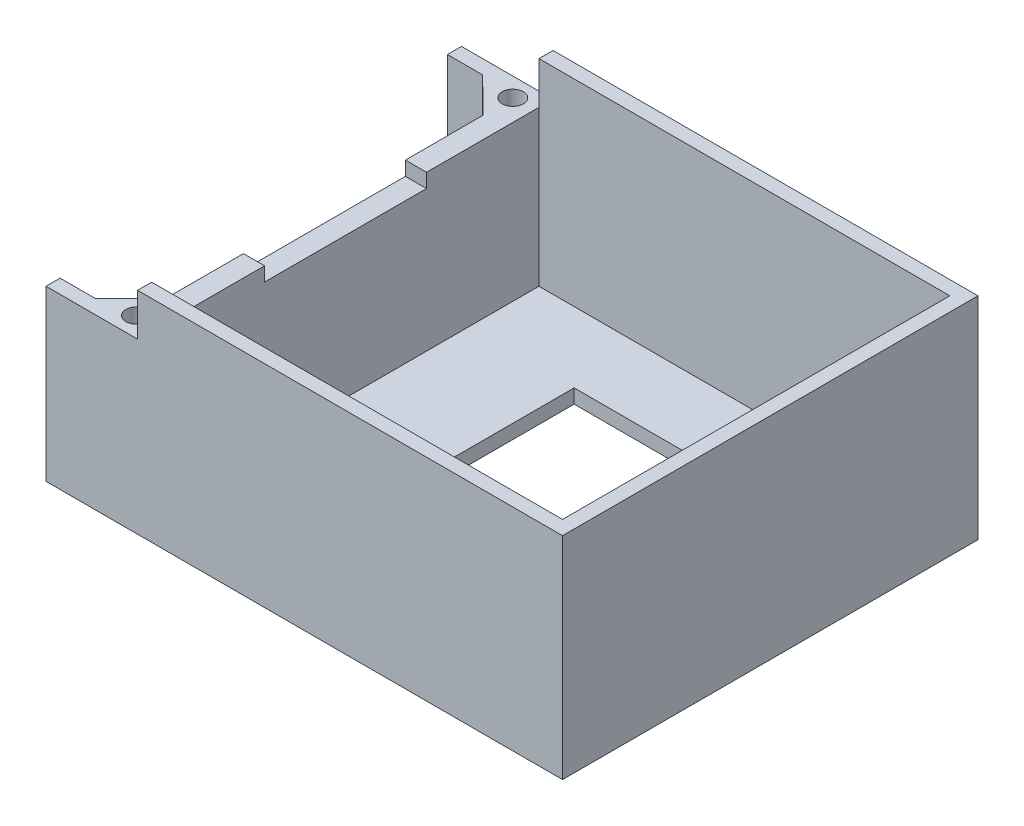
SolidWorks part; units mm, degrees
ref_plane "Front Plane" through (0, 0, 0) normal (0, 0, 1) x (1, 0, 0)
ref_plane "Top Plane" through (0, 0, 0) normal (0, 1, 0) x (1, 0, 0)
ref_plane "Right Plane" through (0, 0, 0) normal (1, 0, 0) x (0, 0, -1)
sketch "Sketch1" plane through (0, 0, 0) normal (0, 1, 0) x (1, 0, 0)
  line L1 (0, 0) -> (70, 0)
  line L2 (0, 0) -> (0, -55)
  line L3 (0, -55) -> (70, -55)
  line L4 (70, 0) -> (70, -55)
  dimension "D1" = 55
  dimension "D2" = 70
extrude "Boss-Extrude1" add sketch "Sketch1" along normal blind 2
sketch "Sketch2" plane through (0, 0, 0) normal (0, 1, 0) x (1, 0, 0)
  line L0 (70, 0) -> (0, 0) construction
  line L1 (-1.3503, 2) -> (72, 2)
  line L2 (-1.3503, 2) -> (-1.3503, -57)
  line L3 (-1.3503, -57) -> (72, -57)
  line L4 (72, 2) -> (72, -57)
  line L5 (0, -55) -> (70, -55) construction
  line L6 (0, 0) -> (0, -55) construction
  line L7 (70, -55) -> (70, 0) construction
  point P5 (-1.3503, 1.4771)
  dimension "D1" = 2
  dimension "D2" = 2
  dimension "D3" = 1.3503
  dimension "D4" = 2
extrude "Boss-Extrude3" add sketch "Sketch2" along normal blind 2
sketch "Sketch3" plane through (0, 2, 0) normal (0, 1, 0) x (1, 0, 0)
  line L0 (-1.3503, 2) -> (72, 2)
  line L1 (72, 2) -> (72, -57)
  line L2 (72, -57) -> (-1.3503, -57)
  line L3 (-1.3503, -57) -> (-1.3503, -55)
  line L4 (-1.3503, 2) -> (-1.3503, -57) construction
  line L5 (-1.3503, -55) -> (70, -55)
  line L6 (70, -55) -> (70, 0)
  line L7 (70, 0) -> (-1.3503, 0)
  line L8 (-1.3503, 0) -> (-1.3503, 2)
  dimension "D1" = 2
  dimension "D2" = 2
extrude "Boss-Extrude4" add sketch "Sketch3" along normal blind 28
sketch "Sketch5" plane through (0, 2, 0) normal (0, 1, 0) x (1, 0, 0)
  line L0 (-1.3503, 0) -> (70, 0) construction
  line L1 (8.6497, 0) -> (11.6497, 0)
  line L2 (8.6497, 0) -> (8.6497, -55)
  line L3 (8.6497, -55) -> (11.6497, -55)
  line L4 (11.6497, 0) -> (11.6497, -55)
  line L5 (70, -55) -> (-1.3503, -55) construction
  line L6 (-1.3503, 0) -> (-1.3503, -55) construction
  line L7 (3.6497, 0) -> (8.6497, -4.9272)
  line L8 (8.6497, -4.9272) -> (8.6497, 0)
  line L9 (3.6497, 0) -> (8.6497, 0)
  line L10 (3.6497, -55) -> (8.6497, -49.9262)
  line L11 (8.6497, -49.9262) -> (8.6497, -55)
  line L12 (3.6497, -55) -> (8.6497, -55)
  line L13 (-1.3503, 0) -> (8.6497, 0) construction
  line L14 (-1.3503, -55) -> (8.6497, -55) construction
  point P17 (3.6497, -55)
  point P18 (8.6497, -4.9272)
  point P20 (0, 0)
  point P21 (0, 0)
  line M8 (-1.3503, -55) -> (70, -55)
  line M10 (70, 0) -> (-1.3503, 0)
  dimension "D1" = 3
  dimension "D2" = 10
  dimension "D3" = 4.9272
extrude "Boss-Extrude5" add sketch "Sketch5" along normal blind 22 contours L4 L2 M10 M8 | L7 L2 M10 | L10 L2 M8
sketch "Sketch14" plane through (0, 30, 0) normal (0, 1, 0) x (1, 0, 0)
  line L1 (-1.3503, 2) -> (11.6497, 2)
  line L2 (-1.3503, 2) -> (-1.3503, 0)
  line L3 (-1.3503, 0) -> (11.6497, 0)
  line L4 (11.6497, 2) -> (11.6497, 0)
  line L5 (-1.3503, -57) -> (11.6497, -57)
  line L6 (-1.3503, -57) -> (-1.3503, -55)
  line L7 (-1.3503, -55) -> (11.6497, -55)
  line L8 (11.6497, -57) -> (11.6497, -55)
extrude "Cut-Extrude5" cut sketch "Sketch14" against normal blind 6
sketch "Sketch15" plane through (0, 24, 0) normal (0, 1, 0) x (1, 0, 0)
  line L0 (3.6497, 0) -> (8.6497, -4.9272) construction
  line L1 (3.6497, -55) -> (8.6497, -49.9262) construction
  circle A2 centre (8.6111, -0.6772) radius 1.5
  circle A3 centre (8.6735, -54.1761) radius 1.5
  dimension "D1" = 3
  dimension "D4" = 3
  dimension "D2" = 3
  dimension "D3" = 4.25
  dimension "D5" = 3
  dimension "D6" = 4.25
extrude "Cut-Extrude6" cut sketch "Sketch15" against normal through all
sketch "Sketch16" plane through (0, 0, 0) normal (0, -1, 0) x (1, 0, 0)
  circle A0 centre (8.6735, 54.1761) radius 2.25
  circle A1 centre (8.6111, 0.6772) radius 2.25
  dimension "D1" = 4.5
  dimension "D2" = 4.5
extrude "Cut-Extrude7" cut sketch "Sketch16" against normal blind 21
sketch "Sketch17" plane through (0, 24, 0) normal (0, 1, 0) x (1, 0, 0)
  line L0 (8.6497, -4.9272) -> (8.6497, -49.9262) construction
  line L1 (8.6497, -38.9634) -> (11.6497, -38.9634)
  line L2 (8.6497, -38.9634) -> (8.6497, -15.9634)
  line L3 (8.6497, -15.9634) -> (11.6497, -15.9634)
  line L4 (11.6497, -38.9634) -> (11.6497, -15.9634)
  line L5 (11.6497, 0) -> (11.6497, -55) construction
  line L7 (11.6497, 0) -> (11.6497, -55) construction
  line L8 (8.6497, -27.4267) -> (11.6497, -27.5) construction
  line L9 (8.6497, -4.9272) -> (8.6497, -49.9262) construction
  line L10 (8.6497, -38.9634) -> (11.6497, -15.9634) construction
  point P8 (11.6497, -27.4634)
  point P17 (10.1497, -27.4634)
  point P18 (10.1497, -27.4634)
  dimension "D1" = 23
extrude "Cut-Extrude8" cut sketch "Sketch17" against normal blind 2
sketch "Sketch18" plane through (0, 2, 0) normal (0, 1, 0) x (1, 0, 0)
  line L0 (40.8249, 0) -> (40.8249, -55) construction
  line L1 (26.6497, -10) -> (63.6497, -10)
  line L2 (26.6497, -10) -> (26.6497, -45)
  line L3 (26.6497, -45) -> (63.6497, -45)
  line L4 (63.6497, -10) -> (63.6497, -45)
  line L5 (40.8249, -10) -> (40.8249, -45) construction
  line L6 (11.6497, 0) -> (70, 0) construction
  line L7 (70, -55) -> (11.6497, -55) construction
  line L8 (11.6497, 0) -> (11.6497, -55) construction
  point P10 (40.8249, -27.5)
  point P13 (40.8249, -27.5)
  dimension "D1" = 15
  dimension "D2" = 35
  dimension "D3" = 37
extrude "Cut-Extrude9" cut sketch "Sketch18" against normal through all
sketch "Sketch19" plane through (0, 0, 0) normal (0, -1, 0) x (1, 0, 0)
  line L0 (-1.3503, 57) -> (72, 57) construction
  line L2 (16.6497, 57) -> (16.6497, -2) construction
  line L3 (72, -2) -> (-1.3503, -2) construction
  line L4 (-1.3503, -2) -> (-1.3503, 57) construction
  text T1 "<b>WPC 2023</b>"
  point P0 (15.7721, -2)
  dimension "D1" = 18
extrude "Cut-Extrude12" cut sketch "Sketch19" against normal blind 1
